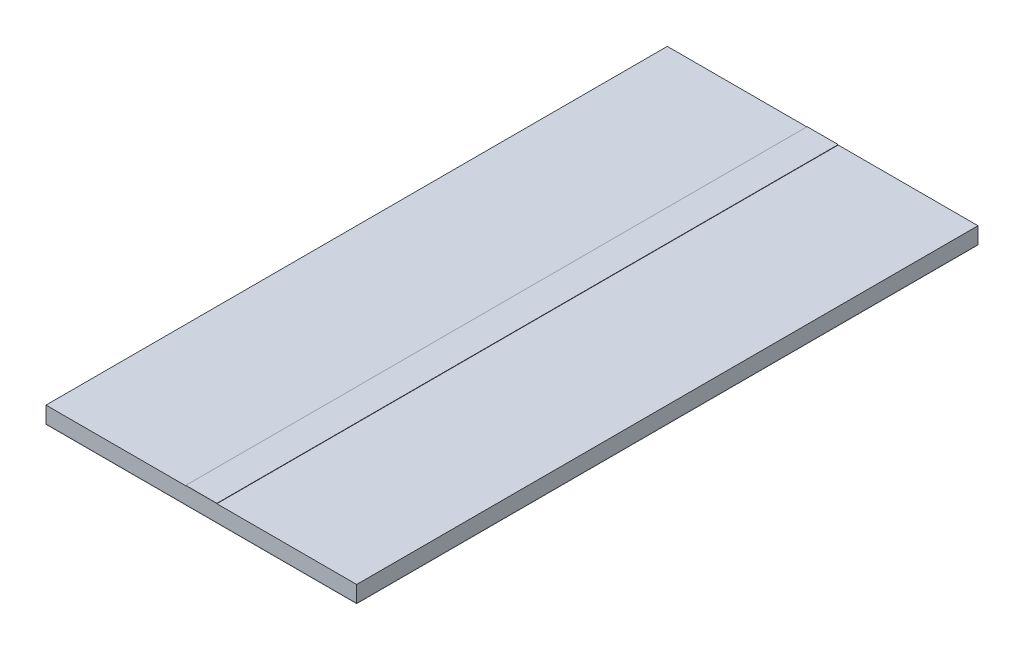
SolidWorks part; units mm, degrees
material "Copper"
ref_plane "Front Plane" through (0, 0, 0) normal (0, 0, 1) x (1, 0, 0)
ref_plane "Top Plane" through (0, 0, 0) normal (0, 1, 0) x (1, 0, 0)
ref_plane "Right Plane" through (0, 0, 0) normal (1, 0, 0) x (0, 0, -1)
sketch "Sketch2" plane through (0, 0, 0) normal (0, 1, 0) x (1, 0, 0)
  line L0 (0, 30) -> (0, -30) construction
  line L1 (-15, -30) -> (15, -30)
  line L2 (-15, -30) -> (-15, 30)
  line L3 (-15, 30) -> (15, 30)
  line L4 (15, -30) -> (15, 30)
  line L5 (-15, -30) -> (15, 30) construction
  line L6 (-15, 30) -> (15, -30) construction
  point P0 (0, 0)
  dimension "D1" = 60
  dimension "D2" = 30
extrude "Boss-Extrude1" add sketch "Sketch2" along normal blind 0.0356
sketch "Sketch3" plane through (0, 0.0356, 0) normal (0, 1, 0) x (1, 0, 0)
  line L1 (-15, 30) -> (15, 30)
  line L2 (-15, 30) -> (-15, -30)
  line L3 (-15, -30) -> (15, -30)
  line L4 (15, 30) -> (15, -30)
extrude "Boss-Extrude2" add sketch "Sketch3" along normal blind 1.57 separate body
sketch "Sketch4" plane through (0, 1.6056, 0) normal (0, 1, 0) x (1, 0, 0)
  line L0 (0, 30) -> (0, -30) construction
  line L1 (15, 30) -> (-15, 30) construction
  line L2 (-15, -30) -> (15, -30) construction
  line L4 (-1.5, -30) -> (1.5, -30)
  line L5 (-1.5, -30) -> (-1.5, 30)
  line L6 (-1.5, 30) -> (1.5, 30)
  line L7 (1.5, -30) -> (1.5, 30)
  line L8 (-1.5, -30) -> (1.5, 30) construction
  line L9 (-1.5, 30) -> (1.5, -30) construction
  point P6 (0, 0)
  dimension "D1" = 3
extrude "Boss-Extrude3" add sketch "Sketch4" along normal blind 0.0356 separate body
